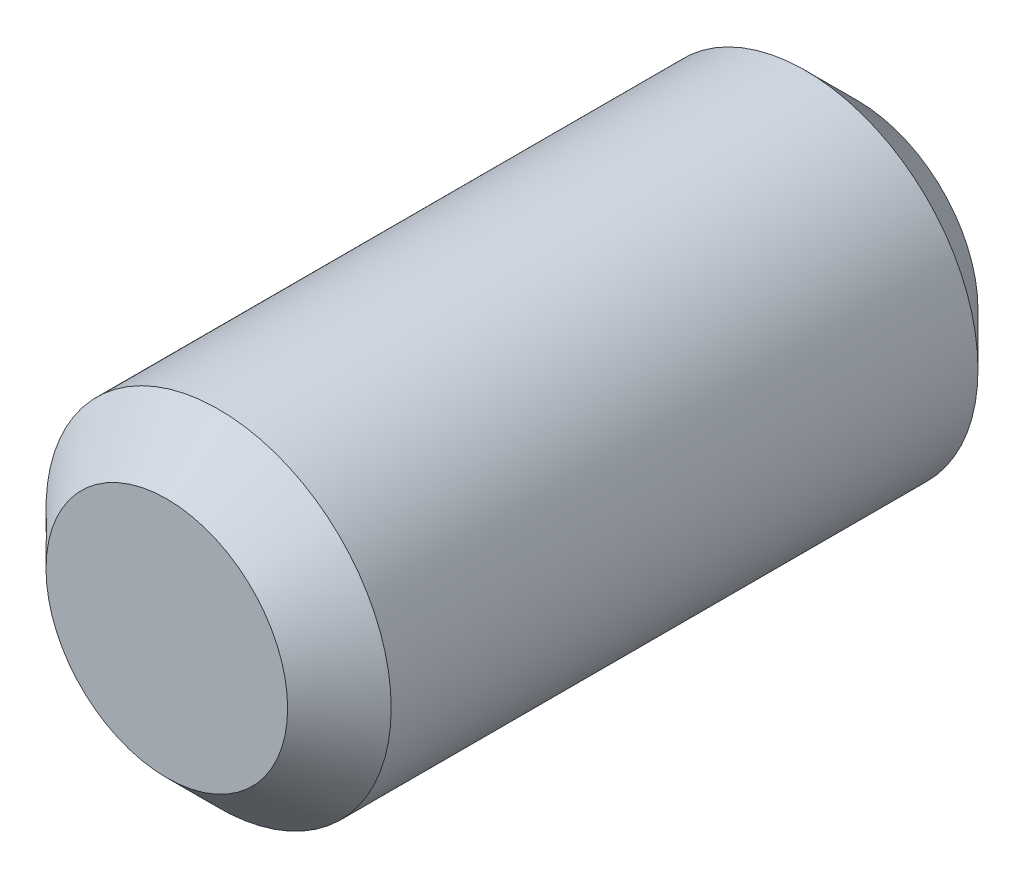
SolidWorks part; units mm, degrees
ref_plane "Front Plane" through (0, 0, 0) normal (0, 0, 1) x (1, 0, 0)
ref_plane "Top Plane" through (0, 0, 0) normal (0, 1, 0) x (1, 0, 0)
ref_plane "Right Plane" through (0, 0, 0) normal (1, 0, 0) x (0, 0, -1)
sketch "Sketch1" plane through (0, 0, 0) normal (0, 0, 1) x (1, 0, 0)
  circle A0 centre (0, 0) radius 1
  dimension "D1" = 2
extrude "Boss-Extrude1" add sketch "Sketch1" along normal blind 4
chamfer "Chamfer1" distance 0.3 angle 45 2 edges at (1, 0, 0) (1, 0, 4)
